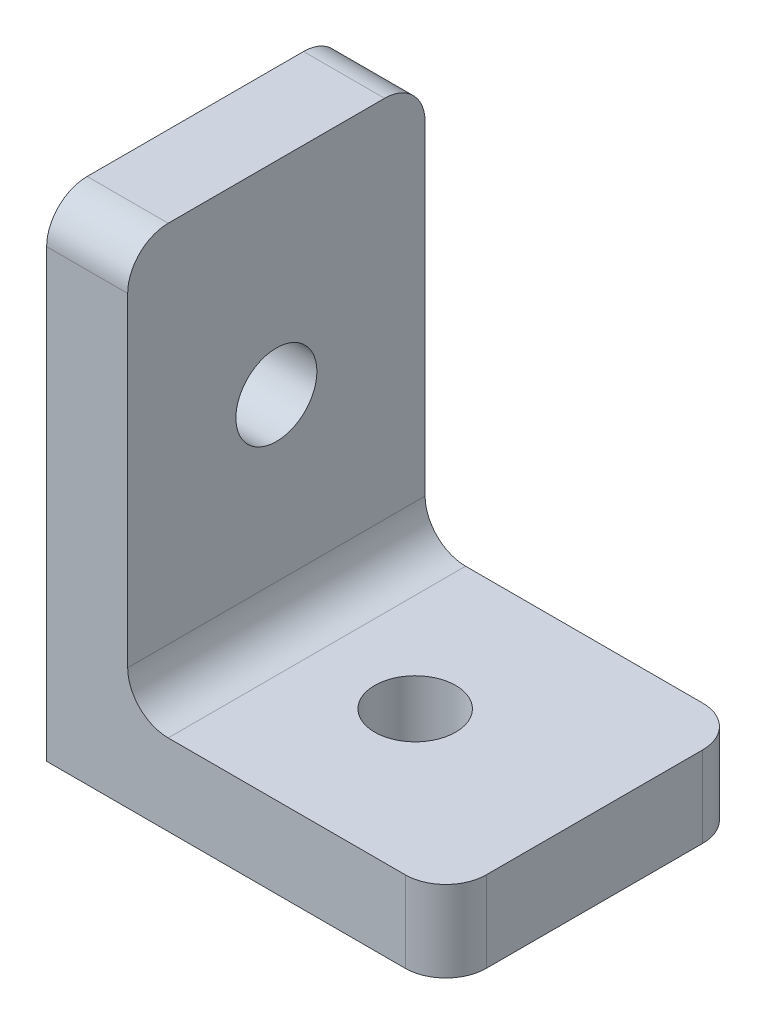
SolidWorks part; units mm, degrees
ref_plane "Front Plane" through (0, 0, 0) normal (0, 0, 1) x (1, 0, 0)
ref_plane "Top Plane" through (0, 0, 0) normal (0, 1, 0) x (1, 0, 0)
ref_plane "Right Plane" through (0, 0, 0) normal (1, 0, 0) x (0, 0, -1)
sketch "Sketch3" plane through (0, 0, 0) normal (0, 1, 0) x (1, 0, 0)
  line L0 (-8.9306, 9.2508) -> (10.7701, 9.2508)
  line L5 (-8.9306, 9.2508) -> (-8.9306, -5.4292)
  line L6 (10.7701, -5.4292) -> (10.7701, 9.2508)
  line L7 (10.7701, -5.4292) -> (-8.9306, -5.4292)
  circle A7 centre (1.9197, 1.9108) radius 2
  point P4 (10.7701, 1.9108)
  dimension "D2" = 14.68
extrude "Boss-Extrude2" add sketch "Sketch3" along normal blind 4
sketch "Sketch5" plane through (0, 4, 0) normal (0, 1, 0) x (1, 0, 0)
  line L0 (-8.9306, -5.4292) -> (10.7701, -5.4292) construction
  line L1 (-8.9306, 9.2508) -> (-4.9306, 9.2508)
  line L2 (-8.9306, 9.2508) -> (-8.9306, -5.4292)
  line L3 (-8.9306, -5.4292) -> (-4.9306, -5.4292)
  line L4 (-4.9306, 9.2508) -> (-4.9306, -5.4292)
  dimension "D1" = 4
extrude "Boss-Extrude3" add sketch "Sketch5" along normal blind 20
sketch "Sketch6" plane through (-4.9306, 0, 0) normal (1, 0, 0) x (0, 0, -1)
  line L1 (-5.4292, 24) -> (9.2508, 24)
  line L2 (-5.4292, 24) -> (-5.4292, 4)
  line L3 (-5.4292, 4) -> (9.2508, 4)
  line L4 (9.2508, 24) -> (9.2508, 4)
  circle A1 centre (1.9108, 14) radius 2
extrude "Cut-Extrude1" cut sketch "Sketch6" against normal blind 10 contours A1
fillet "Fillet1" radius 2 5 edges at (-4.9306, 4, -1.9108) (10.7701, 2, 5.4292) (10.7701, 2, -9.2508) (-6.9306, 24, 5.4292) (-6.9306, 24, -9.2508)
